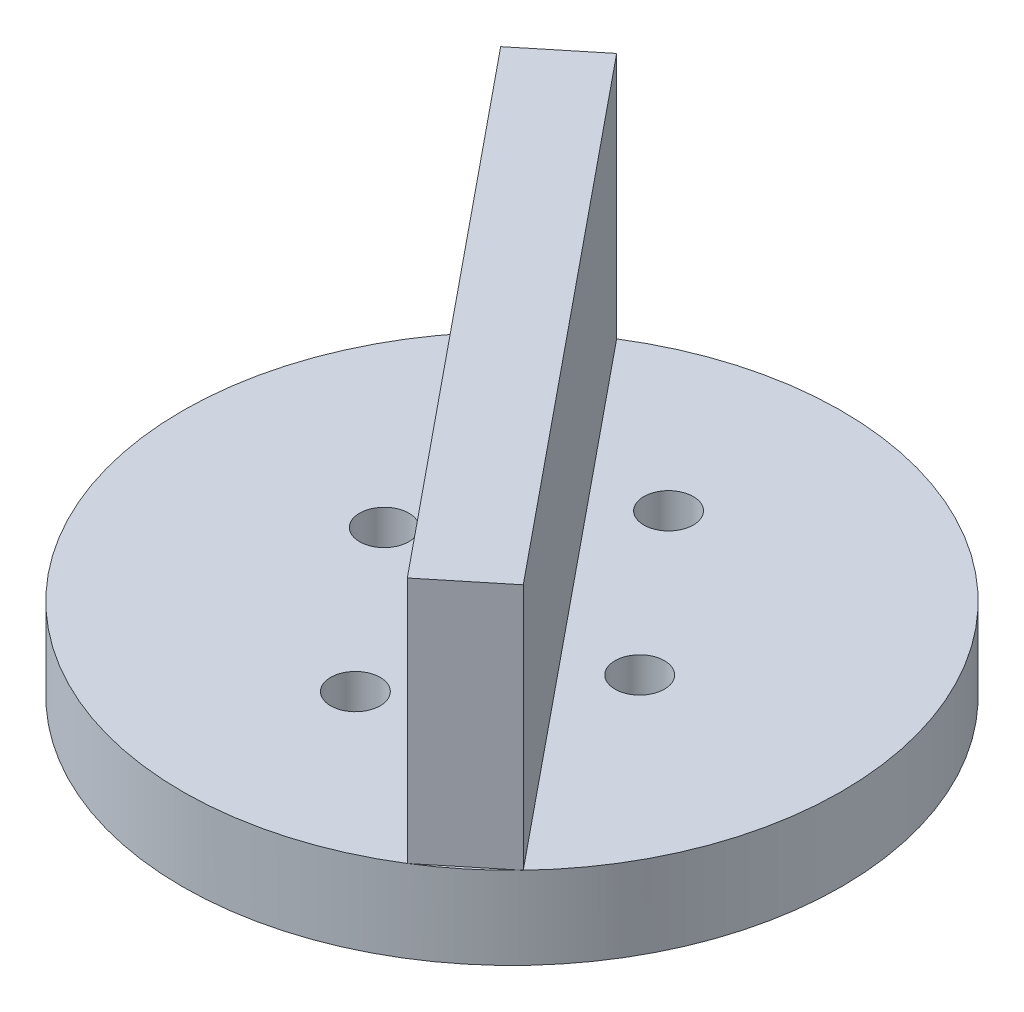
SolidWorks part; units mm, degrees
ref_plane "Спереди" through (0, 0, 0) normal (0, 0, 1) x (1, 0, 0)
ref_plane "Сверху" through (0, 0, 0) normal (0, 1, 0) x (1, 0, 0)
ref_plane "Справа" through (0, 0, 0) normal (1, 0, 0) x (0, 0, -1)
other "Configuration Table"
sketch "Sketch1" plane through (0, 0, 0) normal (0, 1, 0) x (1, 0, 0)
  circle A0 centre (0, 0) radius 20
  dimension "D1" = 40
extrude "Boss-Extrude1" add sketch "Sketch1" along normal blind 5
sketch "Sketch2" plane through (0, 5, 0) normal (0, 1, 0) x (1, 0, 0)
  line L0 (-13.737, 0) -> (13.1462, 0) construction
  line L1 (0, -9.5827) -> (0, 11.0967) construction
  circle A0 centre (0, 9.5) radius 1.5
  circle A1 centre (0, -9.5) radius 1.5
  circle A2 centre (-7.75, 0) radius 1.5
  circle A3 centre (7.75, 0) radius 1.5
  dimension "D1" = 3
  dimension "D2" = 19
  dimension "D3" = 15.5
extrude "Cut-Extrude1" cut sketch "Sketch2" against normal up to next
sketch "Sketch3" plane through (0, 5, 0) normal (0, 1, 0) x (1, 0, 0)
  line L0 (-14.4805, 13.7954) -> (10.6062, -16.9561)
  line L1 (-14.4805, 13.7954) -> (-10.6062, 16.9561)
  line L2 (10.6062, -16.9561) -> (14.4805, -13.7954)
  line L3 (-10.6062, 16.9561) -> (14.4805, -13.7954)
  line L4 (-14.4805, 13.7954) -> (14.4805, -13.7954) construction
  line L5 (10.6062, -16.9561) -> (-10.6062, 16.9561) construction
  line L6 (0, 9.5) -> (-7.75, 0) construction
  line L7 (0, 0) -> (-3.875, 4.75) construction
  circle A0 centre (0, 0) radius 20 construction
  point P1 (0, 0)
  point P12 (-10.298, 17.145)
  dimension "D1" = 5
extrude "Boss-Extrude2" add sketch "Sketch3" along normal blind 15
